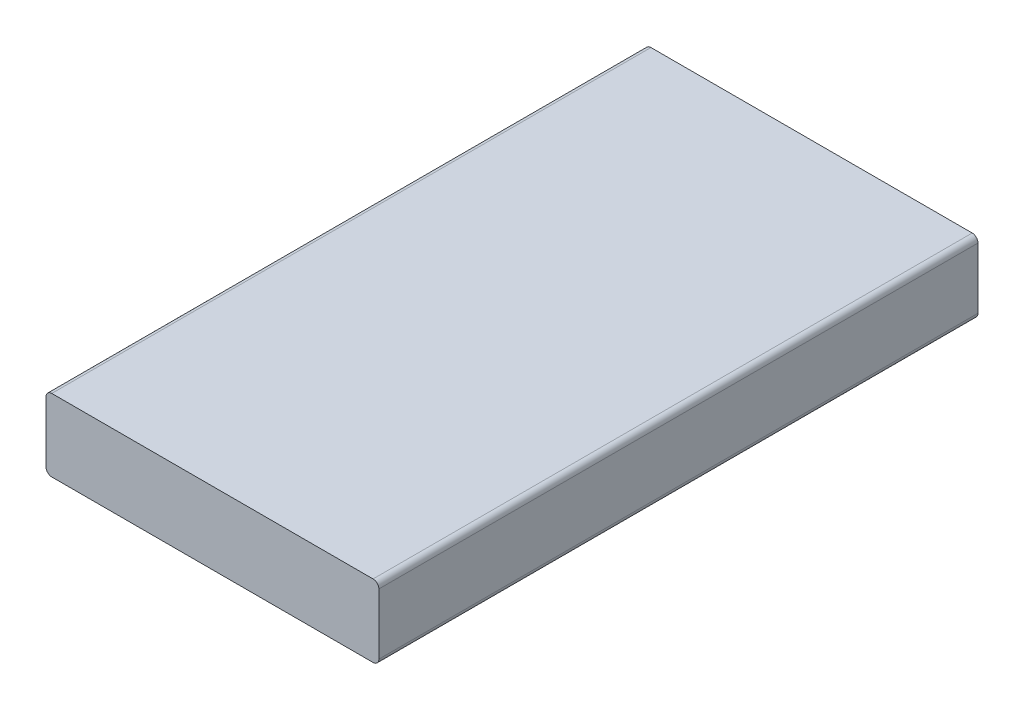
SolidWorks part; units mm, degrees
material "Polyurethane Foam Rigid"
ref_plane "Front Plane" through (0, 0, 0) normal (0, 0, 1) x (1, 0, 0)
ref_plane "Top Plane" through (0, 0, 0) normal (0, 1, 0) x (1, 0, 0)
ref_plane "Right Plane" through (0, 0, 0) normal (1, 0, 0) x (0, 0, -1)
sketch "Sketch1" plane through (0, 0, 0) normal (0, 0, 1) x (1, 0, 0)
  line L1 (-29.3403, 15.8854) -> (85.6597, 15.8854)
  line L2 (-29.3403, 15.8854) -> (-29.3403, -9.1146)
  line L3 (-29.3403, -9.1146) -> (85.6597, -9.1146)
  line L4 (85.6597, 15.8854) -> (85.6597, -9.1146)
  dimension "D1" = 25
  dimension "D2" = 115
extrude "Boss-Extrude1" add sketch "Sketch1" against normal blind 207
fillet "Fillet1" radius 2 4 edges at (85.6597, -9.1146, -103.5) (85.6597, 15.8854, -103.5) (-29.3403, -9.1146, -103.5) (-29.3403, 15.8854, -103.5)
